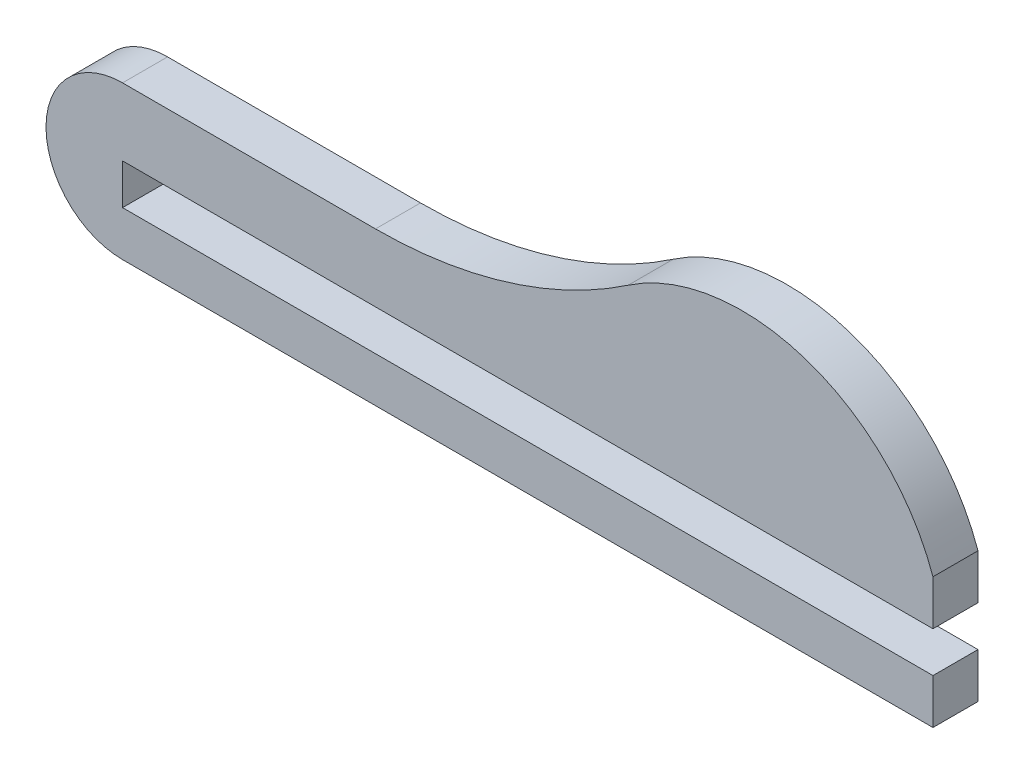
SolidWorks part; units mm, degrees
ref_plane "Alzado" through (0, 0, 0) normal (0, 0, 1) x (1, 0, 0)
ref_plane "Planta" through (0, 0, 0) normal (0, 1, 0) x (1, 0, 0)
ref_plane "Vista lateral" through (0, 0, 0) normal (1, 0, 0) x (0, 0, -1)
sketch "Croquis1" plane through (0, 0, 0) normal (0, 0, 1) x (1, 0, 0)
  line L0 (36, 0) -> (0, 0)
  line L1 (0, 0) -> (0, -1.8)
  line L2 (0, -1.8) -> (36, -1.8)
  line L3 (36, -1.8) -> (36, -3.8)
  line L4 (36, -3.8) -> (0, -3.8)
  line L6 (36, 2) -> (36, 0)
  line L7 (-0.5276, 8) -> (-50000.5276, 8) construction
  line L8 (0, 3) -> (11.2359, 3)
  arc A0 (0, -3.8) -> (0, 3) centre (0, -0.4) cw
  arc A1 (11.2359, 3) -> (22.4627, 6.4483) centre (11.2359, 23) ccw
  arc A2 (22.4627, 6.4483) -> (36, 2) centre (27.5147, -1) cw
  point P17 (36, 3.3882)
  point P18 (0, 0)
  point P19 (0, 0)
  dimension "D3" = 8
  dimension "D6" = 9
  dimension "D7" = 20
  dimension "D1" = 1.8
  dimension "D2" = 36
  dimension "D4" = 2
  dimension "D5" = 3
extrude "Saliente-Extruir1" add sketch "Croquis1" along normal blind 2
